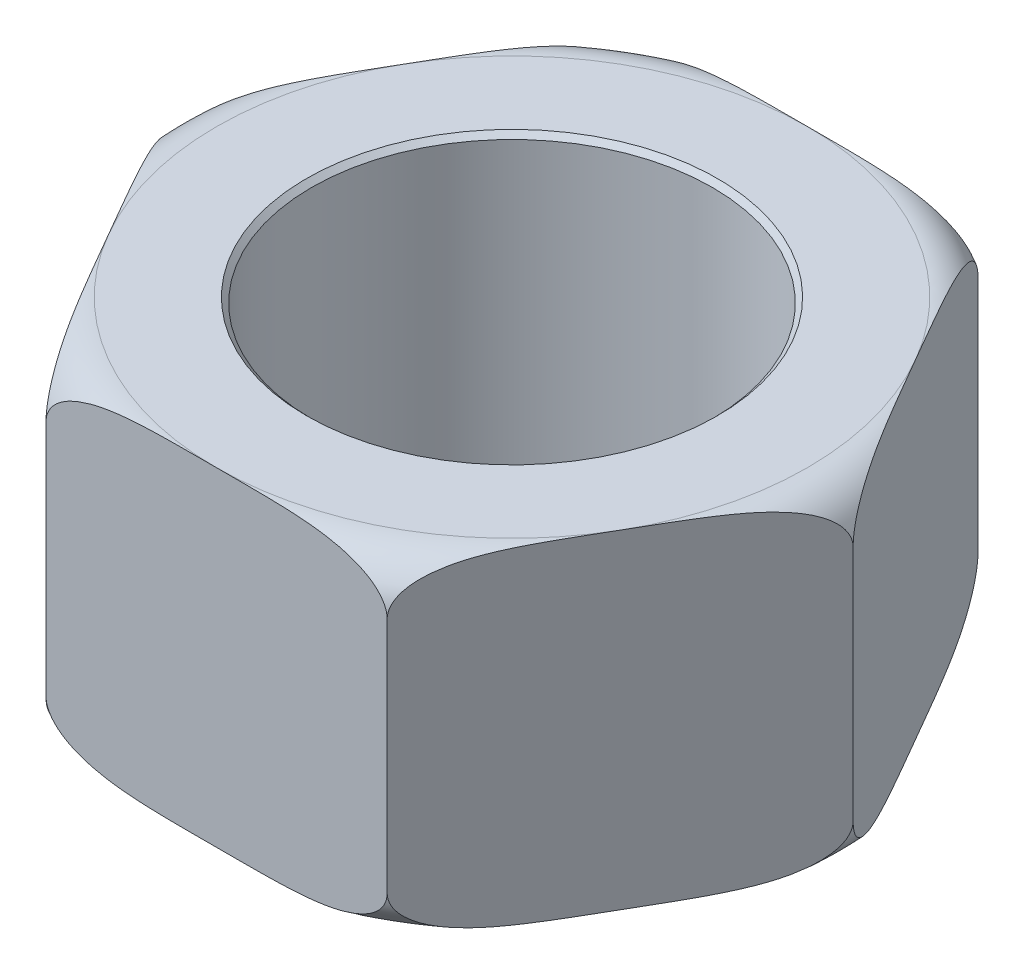
SolidWorks part; units mm, degrees
ref_plane "Front Plane" through (0, 0, 0) normal (0, 0, 1) x (1, 0, 0)
ref_plane "Top Plane" through (0, 0, 0) normal (0, 1, 0) x (1, 0, 0)
ref_plane "Right Plane" through (0, 0, 0) normal (1, 0, 0) x (0, 0, -1)
sketch "Sketch1" plane through (0, 0, 0) normal (0, 1, 0) x (1, 0, 0)
  line L0 (-11.509, 0) -> (11.509, 0) construction
  line L1 (132.7906, 0) -> (66.3953, 115)
  line L2 (66.3953, 115) -> (-66.3953, 115)
  line L3 (-66.3953, 115) -> (-132.7906, 0)
  line L4 (-132.7906, 0) -> (-66.3953, -115)
  line L5 (-66.3953, -115) -> (66.3953, -115)
  line L6 (66.3953, -115) -> (132.7906, 0)
  circle A0 centre (0, 0) radius 115 construction
extrude "Boss-Extrude1" add sketch "Sketch1" along normal mid plane 128
sketch "Sketch3" plane through (0, 0, 0) normal (0, 0, 1) x (1, 0, 0)
  line L0 (-132.7906, 64) -> (-132.7906, -64) construction
  line L1 (-132.7906, 64) -> (-132.7906, 46.2094)
  line L2 (-132.7906, 64) -> (-66.3953, 64) construction
  line L3 (-132.7906, 64) -> (-115, 64)
  line L4 (0, -11.069) -> (0, -12.5043) construction
  line L6 (0, -11.509) -> (0, 11.509) construction
  arc A0 (-132.7906, 46.2094) -> (-115, 64) centre (-115, 46.2094) cw
  dimension "D2" = 7
revolve "Cut-Revolve1" cut sketch "Sketch3" angle 360 about L4
mirror "Mirror1" about plane through (0, 0, 0) normal (0, 1, 0) of "Cut-Revolve1"
sketch "Sketch6" plane through (0, 64, 0) normal (0, 1, 0) x (1, 0, 0)
  circle A0 centre (0, 0) radius 78
  dimension "D1" = 156
extrude "Cut-Extrude1" cut sketch "Sketch6" against normal through all
cosmetic thread "Cosmetic Thread1" parameters "D2"=160
chamfer "Chamfer1" distance 2 angle 45 2 edges at (0, -64, 78) (0, 64, 78)
equation "\"D2@Sketch3\"=\"D1@Sketch1\""
